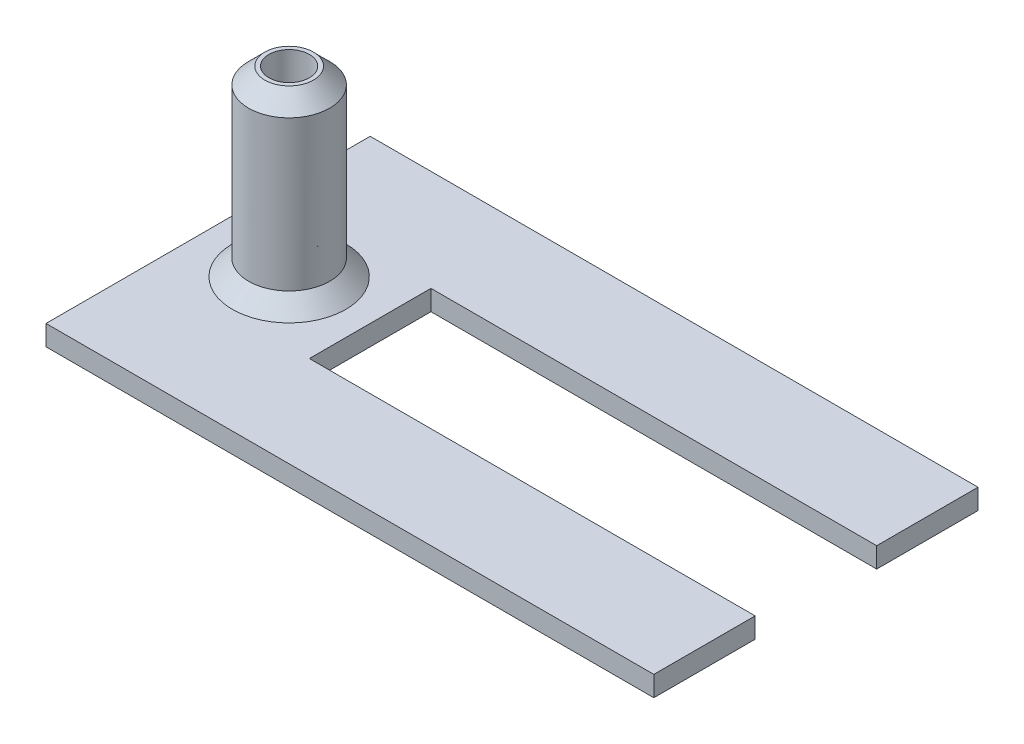
SolidWorks part; units mm, degrees
ref_plane "Front Plane" through (0, 0, 0) normal (0, 0, 1) x (1, 0, 0)
ref_plane "Top Plane" through (0, 0, 0) normal (0, 1, 0) x (1, 0, 0)
ref_plane "Right Plane" through (0, 0, 0) normal (1, 0, 0) x (0, 0, -1)
sketch "Sketch2" plane through (0, 0, 0) normal (0, 1, 0) x (1, 0, 0)
  line L1 (-4, 8) -> (26, 8)
  line L2 (-4, 8) -> (-4, -8)
  line L3 (-4, -8) -> (26, -8)
  line L4 (26, 8) -> (26, -8)
  line L5 (26, 3) -> (4, 3)
  line L6 (26, 3) -> (26, -3)
  line L7 (26, -3) -> (4, -3)
  line L8 (4, 3) -> (4, -3)
  circle A0 centre (0, 0) radius 2
  circle A1 centre (0, 0) radius 1
  point P4 (-4, 0)
  point P13 (4, 0)
  dimension "D3" = 4
  dimension "D4" = 2
  dimension "D1" = 16
  dimension "D2" = 30
  dimension "D5" = 4
  dimension "D6" = 4
  dimension "D7" = 6
sketch "Sketch3" plane through (0, 0, 0) normal (0, 1, 0) x (1, 0, 0)
  line L0 (26, 8) -> (26, 3)
  line L1 (26, 3) -> (4, 3)
  line L2 (4, 3) -> (4, -3)
  line L3 (4, -3) -> (26, -3)
  line L4 (26, -3) -> (26, -8)
  line L5 (-4, -8) -> (26, -8) construction
  line L6 (26, -8) -> (-4, -8)
  line L7 (-4, -8) -> (-4, 8)
  line L8 (-4, 8) -> (26, 8)
  point P6 (0, 0)
extrude "Boss-Extrude1" add sketch "Sketch3" along normal blind 1
sketch "Sketch4" plane through (0, 0, 0) normal (0, 1, 0) x (1, 0, 0)
  circle A0 centre (0, 0) radius 1 construction
  circle A1 centre (0, 0) radius 2 construction
  circle A2 centre (0, 0) radius 1
  circle A3 centre (0, 0) radius 2
extrude "Boss-Extrude2" add sketch "Sketch4" along normal blind 10
chamfer "Chamfer1" distance 0.8 angle 45 2 edges at (0, 1, -2) (0, 10, 2)
